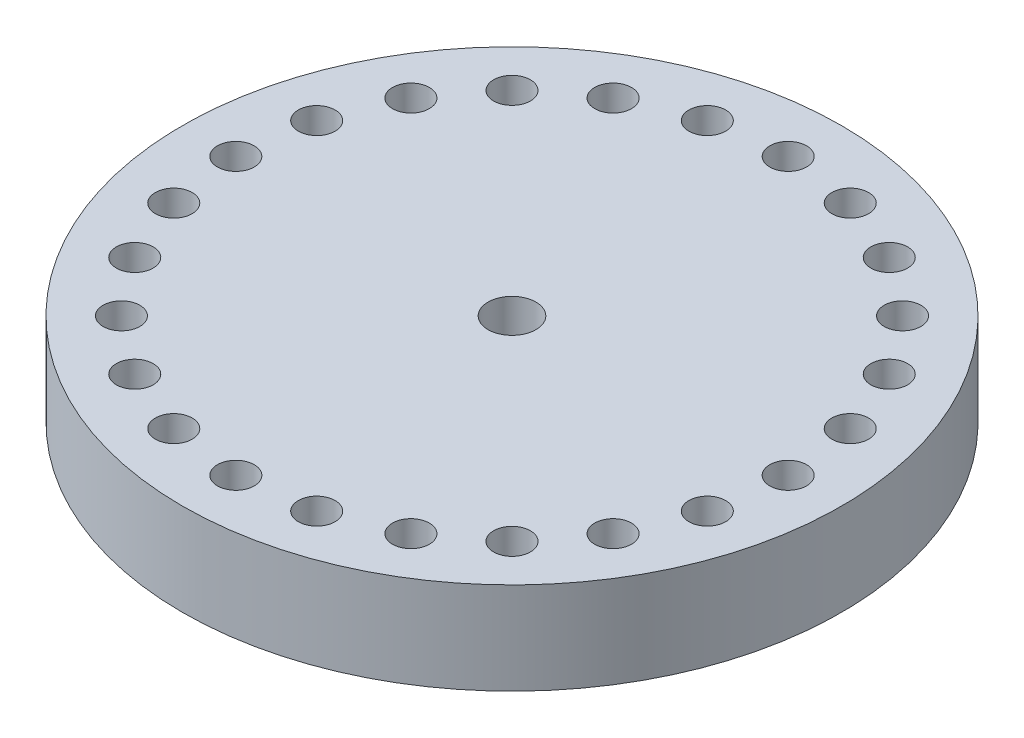
SolidWorks part; units mm, degrees
ref_plane "Front Plane" through (0, 0, 0) normal (0, 0, 1) x (1, 0, 0)
ref_plane "Top Plane" through (0, 0, 0) normal (0, 1, 0) x (1, 0, 0)
ref_plane "Right Plane" through (0, 0, 0) normal (1, 0, 0) x (0, 0, -1)
sketch "Sketch1" plane through (0, 0, 0) normal (0, 1, 0) x (1, 0, 0)
  circle A0 centre (0, 0) radius 20.066 construction
  circle A1 centre (0, 0) radius 45.466
  dimension "D1" = 25.4
extrude "Boss-Extrude1" add sketch "Sketch1" along normal blind 25.4
sketch "Sketch3" plane through (0, 0, 0) normal (0, -1, 0) x (1, 0, 0)
  circle A0 centre (0, 0) radius 20.32
extrude "Cut-Extrude1" cut sketch "Sketch3" against normal blind 12.7
sketch "Sketch4" plane through (0, 0, 0) normal (0, -1, 0) x (1, 0, 0)
  line L0 (0, 0) -> (0, 38.1) construction
  circle A0 centre (0, 38.1) radius 1.778
  dimension "D1" = 38.1
hole_wizard "CSK for 1/4 Flat Head Machine Screw1" positions "Sketch6" profile "Sketch7" countersink size "1/4" standard "ANSI Inch"
sketch "Sketch6" plane through (0, 25.4, 0) normal (0, 1, 0) x (1, 0, 0)
  point P0 (0, 0)
sketch "Sketch7" plane through (0, 25.4, 0) normal (1, 0, 0) x (0, 0, 1)
  line L0 (0, 0) -> (0, 27.3611)
  line L1 (0, 27.3611) -> (3.2639, 25.4)
  line L2 (3.2639, 25.4) -> (3.2639, 3.6524)
  line L3 (3.2639, 3.6524) -> (6.4389, 0)
  line L5 (6.4389, 0) -> (0, 0)
  line L6 (-3.2639, 3.6524) -> (-6.4389, 0) construction
  line L10 (0, 27.3611) -> (-3.2639, 25.4) construction
  line L11 (0, -6.35) -> (0, 107.95) construction
  dimension "Hole Dia." = 6.5278
  dimension "Hole Depth" = 25.4
  dimension "Near C'Sink Dia." = 12.8778
  dimension "Near C'Sink Angle" = 82
  dimension "Drill Angle" = 118
sketch "Sketch8" plane through (0, 25.4, 0) normal (0, 1, 0) x (1, 0, 0)
  circle A0 centre (0, 0) radius 46.9556
extrude "Cut-Extrude2" cut sketch "Sketch8" against normal blind 12.7
extrude "Cut-Extrude3" cut sketch "Sketch4" against normal through all
sketch "Sketch9" plane through (0, 12.7, 0) normal (0, 1, 0) x (1, 0, 0)
  circle A0 centre (0, -38.1) radius 2.54
extrude "Cut-Extrude4" cut sketch "Sketch9" against normal blind 5.08
pattern_circular "CirPattern1" count 24 every 15 about axis through (0, 0, 0) along (0, 1, 0) of "Cut-Extrude3", "Cut-Extrude4"
sketch "Sketch10" plane through (0, 12.7, 0) normal (0, 1, 0) x (1, 0, 0)
  circle A0 centre (0, 0) radius 22.8348
extrude "Boss-Extrude2" add sketch "Sketch10" against normal blind 5.08
sketch "Sketch11" plane through (0, 12.7, 0) normal (0, 1, 0) x (1, 0, 0)
  circle A0 centre (0, 0) radius 3.302
  dimension "D1" = 6.604
extrude "Cut-Extrude5" cut sketch "Sketch11" against normal through all
